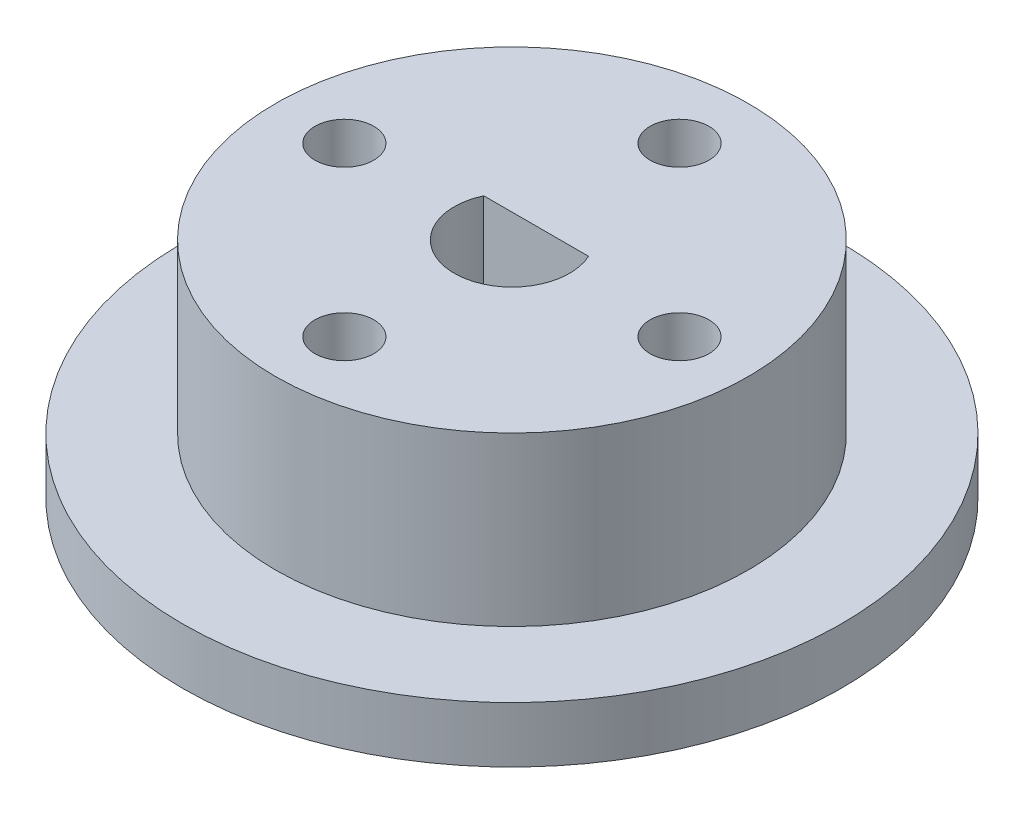
SolidWorks part; units mm, degrees
ref_plane "Front Plane" through (0, 0, 0) normal (0, 0, 1) x (1, 0, 0)
ref_plane "Top Plane" through (0, 0, 0) normal (0, 1, 0) x (1, 0, 0)
ref_plane "Right Plane" through (0, 0, 0) normal (1, 0, 0) x (0, 0, -1)
sketch "Sketch1" plane through (0, 0, 0) normal (0, 1, 0) x (1, 0, 0)
  circle A0 centre (0, 0) radius 12.7
  dimension "D1" = 25.4
extrude "Boss-Extrude1" add sketch "Sketch1" along normal blind 9
sketch "Sketch2" plane through (0, 0, 0) normal (0, 1, 0) x (-1, 0, 0)
  circle A0 centre (0, 0) radius 17.7
  dimension "D1" = 35.4
extrude "Boss-Extrude2" add sketch "Sketch2" against normal blind 3
sketch "Sketch3" plane through (0, 0, 0) normal (0, 1, 0) x (1, 0, 0)
  line L0 (0, -6.6) -> (0, 6.6) construction
  line L1 (-6.6, 0) -> (6.6, 0) construction
  circle A0 centre (0, 0) radius 3.1
  circle A1 centre (-9, 0) radius 1.58
  circle A2 centre (9, 0) radius 1.58
  circle A3 centre (0, 9) radius 1.58
  circle A4 centre (0, -9) radius 1.58
  dimension "D1" = 6.2
  dimension "D2" = 3.16
  dimension "D3" = 9
  dimension "D4" = 3.16
  dimension "D5" = 9
extrude "Cut-Extrude1" cut sketch "Sketch3" along normal through all both and the other way through all
sketch "Sketch4" plane through (0, -3, 0) normal (0, -1, 0) x (1, 0, 0)
  circle A0 centre (0, 0) radius 3.1
  circle A1 centre (0, 0) radius 3.1 construction
extrude "Boss-Extrude3" add sketch "Sketch4" against normal blind 5.5
sketch "Sketch5" plane through (0, 9, 0) normal (0, 1, 0) x (1, 0, 0)
  line L1 (-3.1, 3.1) -> (3.1, 3.1)
  line L2 (-3.1, 3.1) -> (-3.1, 1.3)
  line L3 (-3.1, 1.3) -> (3.1, 1.3)
  line L4 (3.1, 3.1) -> (3.1, 1.3)
  line L5 (-3.1, 3.1) -> (3.1, 1.3) construction
  line L6 (-3.1, 1.3) -> (3.1, 3.1) construction
  circle A0 centre (0, 0) radius 3.1 construction
  circle A1 centre (0, 0) radius 3.1 construction
  point P0 (0, 2.2)
  point P5 (0, 0)
  dimension "D1" = 1.8
extrude "Boss-Extrude4" add sketch "Sketch5" against normal up to surface (6.5 mm away) up to face at (0, 2.5, -3.1)
